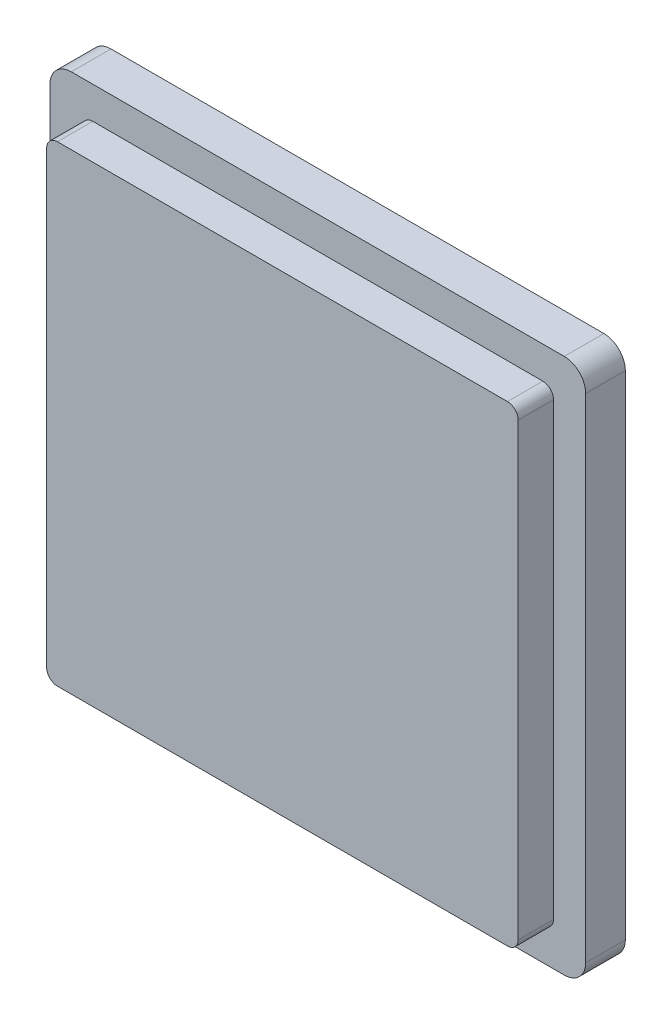
SolidWorks part; units mm, degrees
ref_plane "Plano frontal" through (0, 0, 0) normal (0, 0, 1) x (1, 0, 0)
ref_plane "Plano superior" through (0, 0, 0) normal (0, 1, 0) x (1, 0, 0)
ref_plane "Plano direito" through (0, 0, 0) normal (1, 0, 0) x (0, 0, -1)
sketch "Esboço1" plane through (0, 0, 0) normal (0, 0, 1) x (1, 0, 0)
  line L0 (0, 25) -> (0, 22) construction
  line L1 (-25, 0) -> (-22, 0) construction
  line L2 (-22, -22) -> (-22, 22) construction
  line L3 (0, -25) -> (0, -22) construction
  line L4 (-22, -22) -> (22, -22) construction
  line L5 (23, -25) -> (-23, -25)
  line L6 (25, 0) -> (22, 0) construction
  line L7 (25, 23) -> (25, -23)
  line L8 (22, -22) -> (22, 22) construction
  line L9 (-25, 23) -> (-25, -23)
  line L10 (23, 25) -> (-23, 25)
  line L11 (0, 25) -> (0, -25) construction
  line L12 (25, 0) -> (-25, 0) construction
  line L17 (-22, 22) -> (22, 22) construction
  arc A0 (-23, -25) -> (-25, -23) centre (-23, -23) cw
  arc A1 (25, -23) -> (23, -25) centre (23, -23) cw
  arc A2 (25, 23) -> (23, 25) centre (23, 23) ccw
  arc A3 (-23, 25) -> (-25, 23) centre (-23, 23) ccw
  point P12 (0, 0)
  point P19 (-25, -25)
  point P22 (25, -25)
  point P25 (25, 25)
  point P28 (-25, 25)
  dimension "D1" = 2
extrude "Ressalto-extrusão1" add sketch "Esboço1" along normal blind 3.7
sketch "Esboço3" plane through (0, 0, 3.7) normal (0, 0, 1) x (1, 0, 0)
  line L0 (0, 25) -> (0, 22) construction
  line L1 (-25, 0) -> (-22, 0) construction
  line L2 (-22, -21) -> (-22, 21)
  line L3 (0, -25) -> (0, -22) construction
  line L4 (-21, -22) -> (21, -22)
  line L5 (25, -25) -> (-25, -25) construction
  line L6 (25, 0) -> (22, 0) construction
  line L7 (25, 25) -> (25, -25) construction
  line L8 (22, -21) -> (22, 21)
  line L9 (-25, 25) -> (-25, -25) construction
  line L10 (25, 25) -> (-25, 25) construction
  line L11 (0, 25) -> (0, -25) construction
  line L12 (25, 0) -> (-25, 0) construction
  line L17 (-21, 22) -> (21, 22)
  arc A0 (22, -21) -> (21, -22) centre (21, -21) cw
  arc A1 (-21, -22) -> (-22, -21) centre (-21, -21) cw
  arc A2 (-22, 21) -> (-21, 22) centre (-21, 21) cw
  arc A3 (22, 21) -> (21, 22) centre (21, 21) ccw
  point P12 (0, 0)
  point P19 (22, -22)
  point P22 (-22, -22)
  point P25 (-22, 22)
  point P28 (22, 22)
  dimension "D1" = 1
extrude "Ressalto-extrusão2" add sketch "Esboço3" along normal blind 3.3
